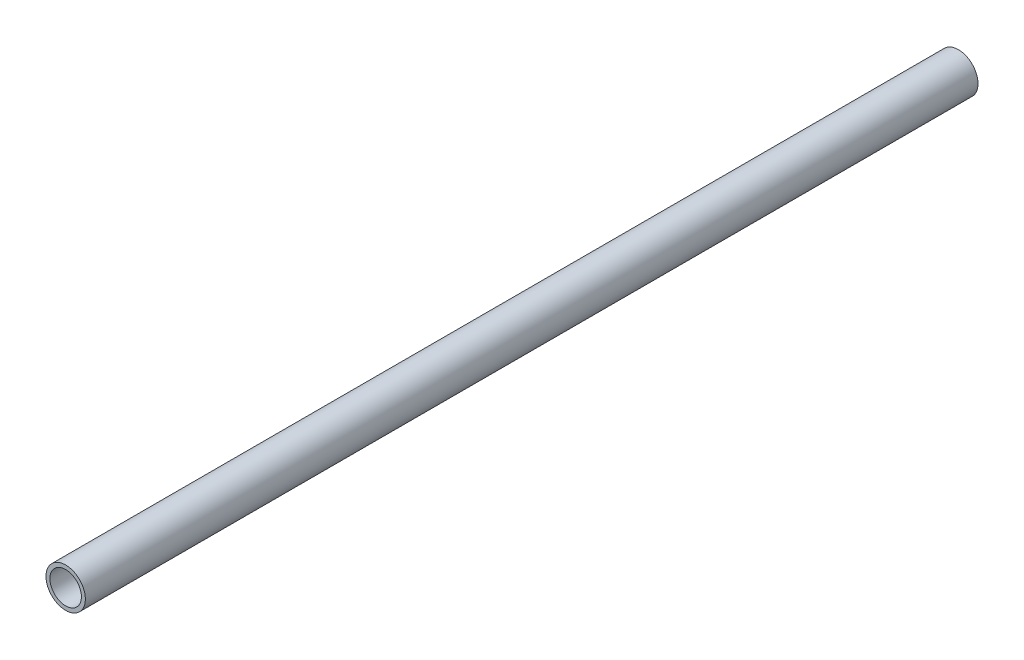
SolidWorks part; units mm, degrees
ref_plane "Face" through (0, 0, 0) normal (0, 0, 1) x (1, 0, 0)
ref_plane "Dessus" through (0, 0, 0) normal (0, 1, 0) x (1, 0, 0)
ref_plane "Droite" through (0, 0, 0) normal (1, 0, 0) x (0, 0, -1)
sketch "Esquisse1" plane through (0, 0, 0) normal (0, 0, 1) x (1, 0, 0)
  circle A0 centre (30, 0) radius 7.5
  circle A1 centre (30, 0) radius 6
  dimension "D1" = 15
  dimension "D2" = 1.5
extrude "Boss.-Extru.1" add sketch "Esquisse1" along normal blind 300 and the other way up to surface (40 mm away)
